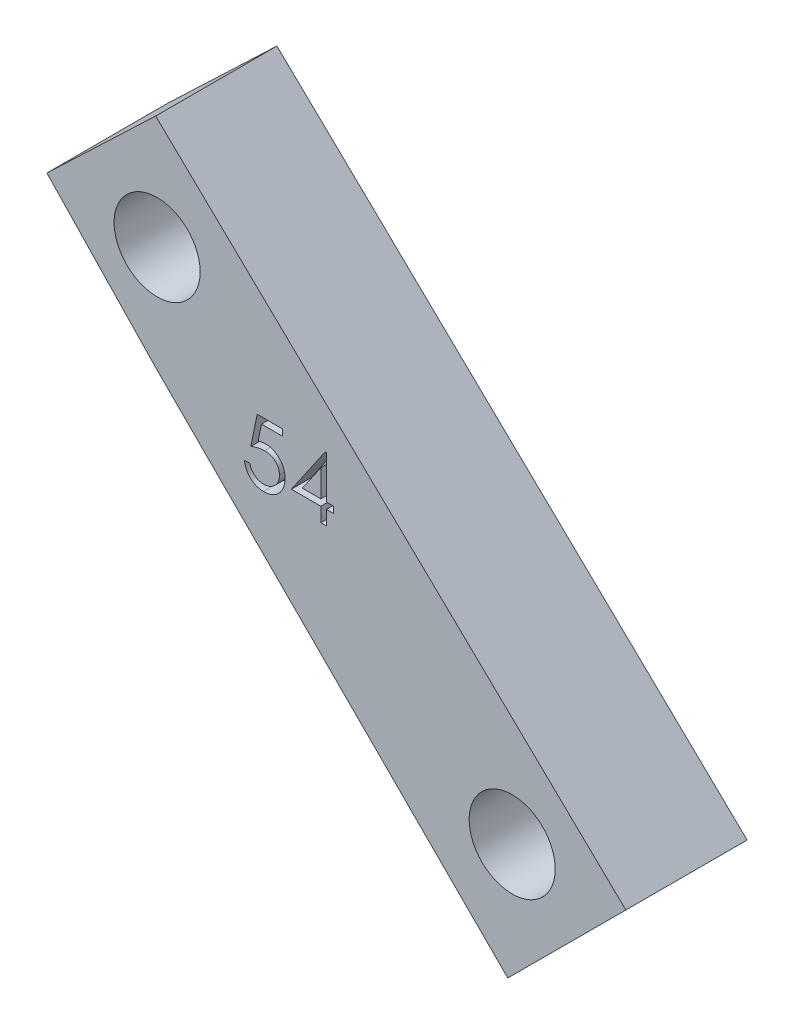
SolidWorks part; units mm, degrees
ref_plane "Front Plane" through (0, 0, 0) normal (0, 0, 1) x (1, 0, 0)
ref_plane "Top Plane" through (0, 0, 0) normal (0, 1, 0) x (1, 0, 0)
ref_plane "Right Plane" through (0, 0, 0) normal (1, 0, 0) x (0, 0, -1)
sketch "Sketch1" plane through (0, 0, 0) normal (0, 0, 1) x (-1, 0, 0)
  line L0 (-149.8064, 88.0436) -> (-144.2985, 82.2676)
  line L1 (-134.4358, 91.6725) -> (-127.4439, 98.3399)
  line L2 (-102.5471, 86.4995) -> (-91.0517, 81.0325)
  line L4 (-81.1984, 94.9179) -> (-74.9984, 94.9179)
  line L7 (-81.1984, 84.9179) -> (-74.9984, 84.9179)
  line L8 (-74.9984, 94.9179) -> (-74.9984, 84.9179)
  line L10 (-102.5385, 76.5028) -> (-81.1984, 84.9179)
  line L11 (-102.5471, 86.4995) -> (-81.1984, 94.9179)
  line L12 (-135.8612, 102.343) -> (-102.5471, 86.4995)
  line L13 (-102.5385, 76.5028) -> (-134.4358, 91.6725)
  line L14 (-135.8612, 102.343) -> (-149.8064, 88.0436)
  line L15 (-134.4358, 91.6725) -> (-149.8602, 76.9641)
  line L16 (-149.8602, 76.9641) -> (-173.8996, 100.0998)
  line L17 (-167.8618, 106.1279) -> (-149.8064, 88.0436)
  line L18 (-167.8618, 106.1279) -> (-173.8996, 100.0998)
  circle A1 centre (-134.7796, 96.3447) radius 2.2
  circle A2 centre (-168.0878, 100.0957) radius 2.2
  circle A3 centre (-149.935, 82.7336) radius 2.2
  circle A4 centre (-102.4484, 81.8835) radius 2.2
  point P3 (-149.935, 82.7336)
  point P25 (-102.5385, 76.5028)
  point P26 (-102.5471, 86.4995)
  point P29 (-135.8612, 102.343)
  point P30 (-149.8064, 88.0436)
  point P35 (-149.8602, 76.9641)
  point P37 (-167.8618, 106.1279)
  point P38 (-173.8996, 100.0998)
  dimension "D2" = 10
  dimension "D3" = 6.2
extrude "Boss-Extrude1" add sketch "Sketch1" along normal blind 6.2 contours L17 L18 L16 L15 L0 A3 A2
sketch "Sketch2" plane through (0, 0, 6.2) normal (0, 0, 1) x (1, 0, 0)
  text T0 "54\r\n"
extrude "Cut-Extrude1" cut sketch "Sketch2" against normal blind 1
